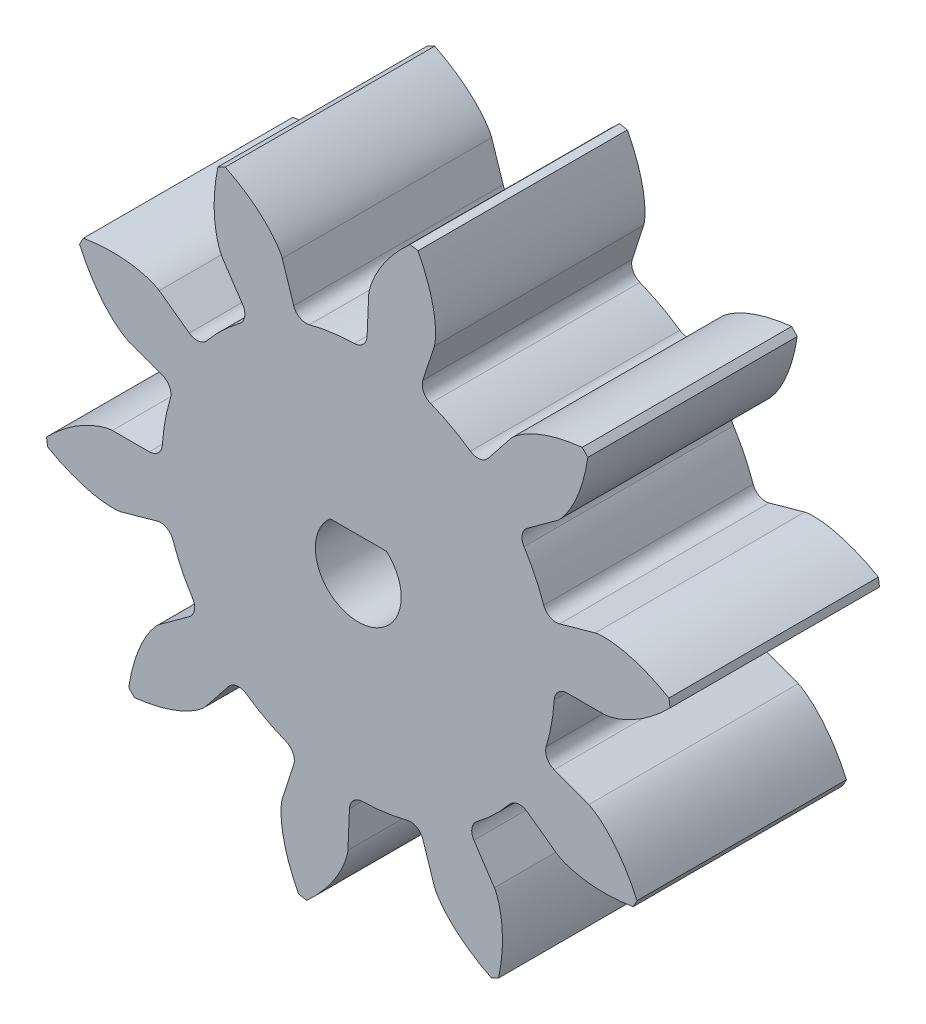
SolidWorks part; units mm, degrees
ref_plane "Front Plane" through (0, 0, 0) normal (0, 0, 1) x (1, 0, 0)
ref_plane "Top Plane" through (0, 0, 0) normal (0, 1, 0) x (1, 0, 0)
ref_plane "Right Plane" through (0, 0, 0) normal (1, 0, 0) x (0, 0, -1)
sketch "Sketch1" plane through (0, 0, 0) normal (0, 0, 1) x (1, 0, 0)
  line L0 (11.7462, 0) -> (9.375, 0)
  line L1 (14.8615, 2.0335) -> (-14.8615, -2.0335)
  line L2 (0, 0) -> (12.4986, 0.1863) construction
  circle A0 centre (0, 0) radius 11.7462 construction
  circle A1 centre (0, 0) radius 15
  circle A2 centre (0, 0) radius 9.375
  circle A3 centre (0, 0) radius 12.5 construction
  spline S0 degree 4 poles (11.7462, 0) (11.7548, 0.0002) (11.7792, 0.0013) (11.8251, 0.0056) (11.8997, 0.0157) (11.9942, 0.0334) (12.1154, 0.0615) (12.2568, 0.1013) (12.4106, 0.1522) (12.5757, 0.215) (12.7384, 0.2842) (12.8986, 0.3593) (13.0561, 0.4395) (13.2442, 0.5429) (13.4661, 0.6756) (13.7194, 0.8429) (13.9992, 1.0471) (14.2756, 1.27) (14.5402, 1.5014) (14.7983, 1.7485) (15.0415, 1.9969) (15.284, 2.2678) (15.5027, 2.5246) (15.7358, 2.8258) (15.9205, 3.0729) (16.1508, 3.4126) (16.2828, 3.6172) (16.4326, 3.8613) (16.4966, 3.972) (16.5361, 4.0402) knots 0 0 0 0 0 0.005377 0.015084 0.028532 0.04661 0.064855 0.092111 0.119476 0.146842 0.174209 0.201575 0.228941 0.256307 0.307035 0.361767 0.4165 0.471232 0.525964 0.580697 0.635429 0.690161 0.744894 0.799626 0.854358 0.909091 0.954545 1 1 1 1 1 construction
  spline S1 degree 4 poles (11.7462, 0) (11.7548, 0.0002) (11.7792, 0.0013) (11.8251, 0.0056) (11.8997, 0.0157) (11.9942, 0.0334) (12.1154, 0.0615) (12.2568, 0.1013) (12.4106, 0.1522) (12.5757, 0.215) (12.7384, 0.2842) (12.8986, 0.3593) (13.0561, 0.4395) (13.2442, 0.5429) (13.4661, 0.6756) (13.7194, 0.8429) (13.9992, 1.0471) (14.2756, 1.27) (14.5402, 1.5014) (14.7983, 1.7485) (15.0415, 1.9969) (15.284, 2.2678) (15.5027, 2.5246) (15.7358, 2.8258) (15.9205, 3.0729) (16.1009, 3.3389) (16.1871, 3.47) (16.2305, 3.5376) knots 0 0 0 0 0 0.005377 0.015084 0.028532 0.04661 0.064855 0.092111 0.119476 0.146842 0.174209 0.201575 0.228941 0.256307 0.307035 0.361767 0.4165 0.471232 0.525964 0.580697 0.635429 0.690161 0.744894 0.799626 0.854358 0.909091 0.909091 0.909091 0.909091 0.909091
  dimension "D1" = 23.4923
  dimension "D2" = 30
  dimension "D3" = 18.75
  dimension "D5" = 25
  dimension "D4" = 6.937
extrude "Boss-Extrude3" add sketch "Sketch1" along normal blind 10 contours L1 A2 | A2 L1 | L0 S1 A1 L1 A2
mirror "Mirror2" about plane through (0, 0, 10) normal (0.1356, -0.9908, 0) of "Boss-Extrude3"
fillet "Fillet1" radius 0.625 2 edges at (9.0304, 2.5184, 5) (9.375, 0, 5)
pattern_circular "CirPattern8" count 10 over 360 about axis through (0, 0, 10) along (0, 0, -1) of "Boss-Extrude3", "Mirror2", "Fillet1"
sketch "Sketch3" plane through (0, 0, 10) normal (0, 0, 1) x (1, 0, 0)
  circle A0 centre (0, 0) radius 2.05
  dimension "D1" = 4.1
extrude "Cut-Extrude2" cut sketch "Sketch3" against normal through all
sketch "Sketch4" plane through (0, 0, 0) normal (0, 0, -1) x (-1, 0, 0)
  line L0 (-1.3416, 1.55) -> (1.3416, 1.55)
  circle A0 centre (0, 0) radius 2.05 construction
  circle A1 centre (0, 0) radius 2.05
  dimension "D1" = 1.55
extrude "Boss-Extrude4" add sketch "Sketch4" against normal up to surface (10 mm away) contours L0 A1
equation "\"d\"= 25mm'Pitch diameter"
equation "\"N\"= 10'Number of teeth"
equation "\"bl\"= 0.9mm'Backlash"
equation "\"pa\"= 20deg'Pressure angle (deg)"
equation "\"pc\"= ( 3.1415 * \"d\" ) / \"N\"\t'Circular pitch"
equation "\"m\"= \"d\" / \"N\"\t\t\t'module"
equation "\"P\"= \"N\" / \"d\"\t\t\t'Diametral pitch"
equation "\"a\"= 1/\"P\"\t\t\t'Addendum distance"
equation "\"b\"= 1.25 / \"P\"'Dedendum distance"
equation "\"rb\"= (\"d\"/2)*cos(\"pa\")\t\t'base circle radius"
equation "\"cp\"= 3.1415/\"P\"\t\t'Circular pitch"
equation "\"t\"= ( \"cp\" / 2 ) - \"bl\"'tooth tickness"
equation "\"c\"=\"b\"-\"a\"\t\t\t'Clearance"
equation "\"facewidth\"= 10mm'face width"
equation "\"rbd\"= \"rb\" * 2'base circle diameter"
equation "\"D1@Sketch1\"=\"rbd\""
equation "\"D2@Sketch1\"= \"d\" + (\"a\" * 2)"
equation "\"D3@Sketch1\" = \"ded\""
equation "\"D4@Sketch1\"= ((\"t\" /2) / (\"d\"/2)) * (180/3.1415)"
equation "\"D1@Boss-Extrude3\"=\"facewidth\""
equation "\"D1@Fillet1\"=\"c\""
equation "\"D1@CirPattern8\"=\"N\""
equation "\"D5@Sketch1\"=\"d\""
equation "\"ded1\"= \"d\" - 2 * ( ( ( \"d\" / 2 ) - \"rb\" ) + ( 0.5 * ( 1.25 / \"P\" ) ) )"
equation "\"ded2\"= \"d\" - ( \"b\" * 2 )"
equation "\"ded\"= IIF ( \"rb\" < ( \"ded2\" / 2 ) , \"ded1\" , \"ded2\" )"
equation "\"shaftdia\"= 4.1mm"
equation "\"D1@Sketch3\"=\"shaftdia\""
